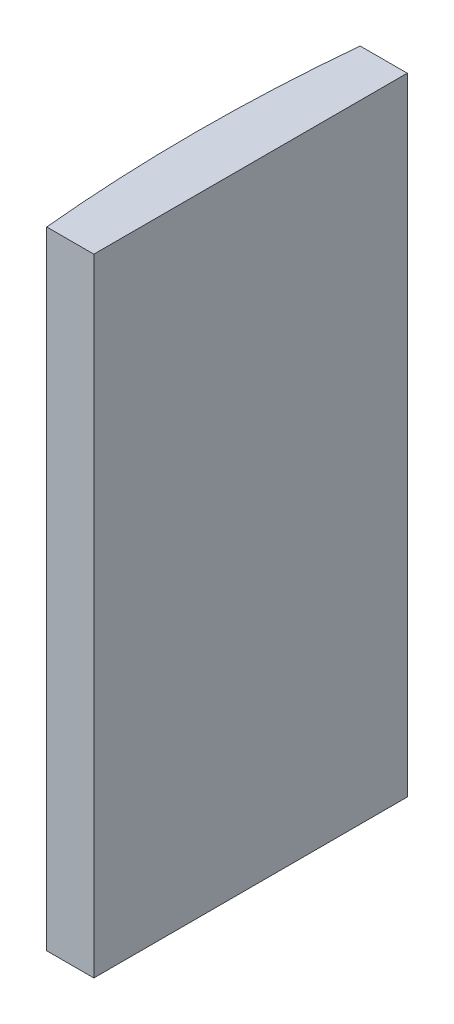
SolidWorks part; units mm, degrees
ref_plane "前视基准面" through (0, 0, 0) normal (0, 0, 1) x (1, 0, 0)
ref_plane "上视基准面" through (0, 0, 0) normal (0, 1, 0) x (1, 0, 0)
ref_plane "右视基准面" through (0, 0, 0) normal (1, 0, 0) x (0, 0, -1)
sketch "草图1" plane through (0, 0, 0) normal (0, 1, 0) x (1, 0, 0)
  line L0 (10.7432, 0) -> (-607.0701, 0) construction
  line L1 (-98.5601, 10) -> (-95.5548, 10)
  line L2 (-98.5601, -10) -> (-95.5548, -10)
  line L3 (-95.5548, 10) -> (-95.5548, -10)
  arc A0 (-98.5601, 10) -> (-98.5601, -10) centre (4.3552, 0) ccw
  point P19 (-99.0448, 0)
  point P20 (-95.5548, 0)
  dimension "D2" = 10
  dimension "D3" = 103.4
  dimension "D4" = 3.49
  dimension "D1" = 10
extrude "凸台-拉伸1" add sketch "草图1" along normal blind 40
